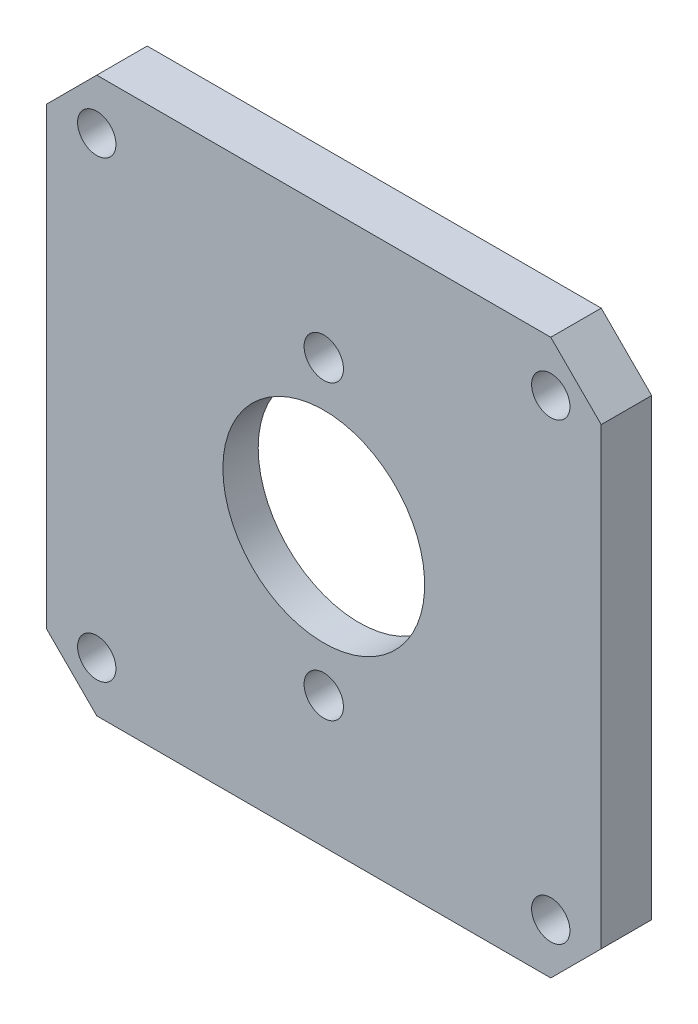
SolidWorks part; units mm, degrees
ref_plane "Front Plane" through (0, 0, 0) normal (0, 0, 1) x (1, 0, 0)
ref_plane "Top Plane" through (0, 0, 0) normal (0, 1, 0) x (1, 0, 0)
ref_plane "Right Plane" through (0, 0, 0) normal (1, 0, 0) x (0, 0, -1)
sketch "Sketch1" plane through (0, 0, 0) normal (0, 0, 1) x (1, 0, 0)
  line L1 (-27.5, -27.5) -> (27.5, -27.5)
  line L2 (-27.5, -27.5) -> (-27.5, 27.5)
  line L3 (-27.5, 27.5) -> (27.5, 27.5)
  line L4 (27.5, -27.5) -> (27.5, 27.5)
  line L5 (-27.5, -27.5) -> (27.5, 27.5) construction
  line L6 (-27.5, 27.5) -> (27.5, -27.5) construction
  point P0 (0, 0)
  dimension "D1" = 55
  dimension "D2" = 55
extrude "Boss-Extrude1" add sketch "Sketch1" along normal blind 5 contours L3 L4 L1 L2
chamfer "Chamfer1" distance 5 angle 45 4 edges at (-27.5, -27.5, 2.5) (27.5, -27.5, 2.5) (27.5, 27.5, 2.5) (-27.5, 27.5, 2.5)
sketch "Sketch2" plane through (0, 0, 0) normal (0, 0, -1) x (-1, 0, 0)
  line L0 (22.5, 27.5) -> (-22.5, 27.5) construction
  line L1 (-27.5, -22.5) -> (-27.5, 22.5) construction
  line L2 (0, 0) -> (40.6962, 0) construction
  circle A0 centre (0, 14.5) radius 1.95
  circle A1 centre (-22.5, 22.5) radius 1.9
  circle A3 centre (22.5, 22.5) radius 1.9
  circle A5 centre (22.5, -22.5) radius 1.9
  circle A7 centre (-22.5, -22.5) radius 1.9
  circle A8 centre (0, 0) radius 10
  circle A9 centre (-14.5, 0) radius 1.95 [skipped]
  circle A10 centre (0, -14.5) radius 1.95 [skipped]
  circle A11 centre (14.5, 0) radius 1.95 [skipped]
  circle A12 centre (0, -14.5) radius 1.95
  point P24 (0, 0)
  dimension "D1" = 14.5
  dimension "D3" = 3.9
  dimension "D4" = 3.8
  dimension "D8" = 20
  dimension "D2" = 0
  dimension "D5" = 5
  dimension "D6" = 5
  dimension "D7" = 4
extrude "Cut-Extrude1" cut sketch "Sketch2" against normal blind 10
sketch "Sketch3" plane through (0, 0, 0) normal (0, 0, -1) x (-1, 0, 0)
  circle A0 centre (0, 0) radius 17.5
  dimension "D1" = 35
extrude "Cut-Extrude2" cut sketch "Sketch3" against normal blind 1.5
